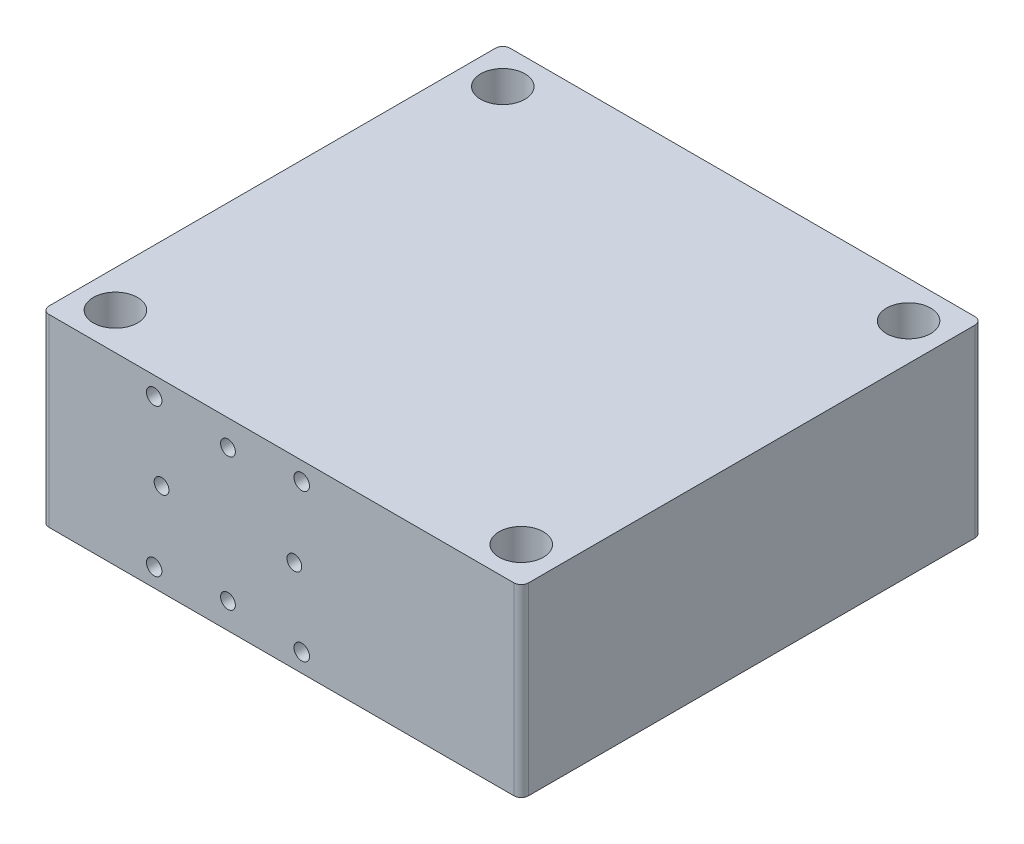
SolidWorks part; units mm, degrees
ref_plane "Front" through (0, 0, 0) normal (0, 0, 1) x (1, 0, 0)
ref_plane "Top" through (0, 0, 0) normal (0, 1, 0) x (1, 0, 0)
ref_plane "Right" through (0, 0, 0) normal (1, 0, 0) x (0, 0, -1)
sketch "草图1" plane through (0, 0, 0) normal (0, 1, 0) x (1, 0, 0)
  line L1 (-65, 62.5) -> (65, 62.5)
  line L2 (-65, 62.5) -> (-65, -62.5)
  line L3 (-65, -62.5) -> (65, -62.5)
  line L4 (65, 62.5) -> (65, -62.5)
  line L5 (-65, 62.5) -> (65, -62.5) construction
  line L6 (-65, -62.5) -> (65, 62.5) construction
  point P0 (0, 0)
  dimension "D1" = 125
  dimension "D2" = 130
extrude "凸台-拉伸1" add sketch "草图1" along normal blind 50
sketch "草图2" plane through (0, 50, 0) normal (0, 1, 0) x (1, 0, 0)
  line L1 (-55, 52.5) -> (55, 52.5) construction
  line L2 (-55, 52.5) -> (-55, -52.5) construction
  line L3 (-55, -52.5) -> (55, -52.5) construction
  line L4 (55, 52.5) -> (55, -52.5) construction
  line L5 (-55, 52.5) -> (55, -52.5) construction
  line L6 (-55, -52.5) -> (55, 52.5) construction
  circle A0 centre (-55, 52.5) radius 6
  circle A1 centre (55, 52.5) radius 6
  circle A2 centre (55, -52.5) radius 6
  circle A3 centre (-55, -52.5) radius 6
  point P0 (0, 0)
  dimension "D3" = 12
  dimension "D4" = 12
  dimension "D5" = 12
  dimension "D6" = 12
  dimension "D1" = 105
  dimension "D2" = 110
extrude "切除-拉伸1" cut sketch "草图2" against normal through all
fillet "圆角1" radius 2 4 edges at (-65, 25, 62.5) (-65, 25, -62.5) (65, 25, -62.5) (65, 25, 62.5)
sketch "草图4" plane through (0, 0, 0) normal (0, -1, 0) x (1, 0, 0)
  line L0 (-65, -60.5) -> (-65, 60.5) construction
  line L1 (-63, 62.5) -> (63, 62.5) construction
  circle A0 centre (-35, -27.5) radius 11.5
  circle A1 centre (5, 2.5) radius 11.5
  dimension "D1" = 23
  dimension "D2" = 30
  dimension "D3" = 70
  dimension "D4" = 90
  dimension "D5" = 60
extrude "切除-拉伸2" cut sketch "草图4" against normal blind 2
hole_wizard "大小mm 暗销孔4" positions "草图6" profile "草图7" hole size "Ø1.0" standard "GB"
sketch "草图6" plane through (0, 2, 0) normal (0, -1, 0) x (-1, 0, 0)
  point P0 (-5, -2.5)
sketch "草图7" plane through (5, 2, 2.5) normal (1, 0, 0) x (0, 0, -1)
  line L0 (0, 0) -> (0, 28.3047)
  line L1 (0, 28.3047) -> (5.5, 25)
  line L2 (5.5, 25) -> (5.5, 0)
  line L5 (5.5, 0) -> (0, 0)
  line L10 (0, 28.3047) -> (-5.5, 25) construction
  line L11 (0, -6.35) -> (0, 107.95) construction
  dimension "孔直径" = 11
  dimension "孔深度" = 25
  dimension "导头角度" = 118
hole_wizard "大小mm 暗销孔4" positions "草图8" profile "草图9" hole size "Ø1.0" standard "GB"
sketch "草图8" plane through (0, 2, 0) normal (0, -1, 0) x (-1, 0, 0)
  point P0 (35, 27.5)
sketch "草图9" plane through (-35, 2, -27.5) normal (1, 0, 0) x (0, 0, -1)
  line L0 (0, 0) -> (0, 28.3047)
  line L1 (0, 28.3047) -> (5.5, 25)
  line L2 (5.5, 25) -> (5.5, 0)
  line L5 (5.5, 0) -> (0, 0)
  line L10 (0, 28.3047) -> (-5.5, 25) construction
  line L11 (0, -6.35) -> (0, 107.95) construction
  dimension "孔直径" = 11
  dimension "孔深度" = 25
  dimension "导头角度" = 118
sketch "草图5" plane through (0, 0, 62.5) normal (0, 0, 1) x (1, 0, 0)
  line L0 (-14.5, 48.5615) -> (-14.5, 1.4385) construction
  line L1 (-34.5, 45) -> (5.5, 45) construction
  line L2 (-34.5, 45) -> (-34.5, 5) construction
  line L3 (-34.5, 5) -> (5.5, 5) construction
  line L4 (5.5, 45) -> (5.5, 5) construction
  line L5 (-38.4133, 25) -> (9.4133, 25) construction
  line L6 (-63, 50) -> (-63, 0) construction
  line L7 (-63, 0) -> (63, 0) construction
  circle A0 centre (-14.5, 25) radius 18 construction
  circle A1 centre (-14.5, 43) radius 2
  circle A2 centre (3.5, 25) radius 2
  circle A3 centre (-14.5, 7) radius 2
  circle A4 centre (-32.5, 25) radius 2
  point P22 (0, 0)
  dimension "D3" = 36
  dimension "D4" = 4
  dimension "D5" = 4
  dimension "D6" = 4
  dimension "D7" = 4
  dimension "D1" = 40
  dimension "D2" = 40
  dimension "D8" = 30.5
  dimension "D9" = 5
  dimension "D10" = 20
  dimension "D11" = 20
hole_wizard "M5 螺纹孔1" positions "草图10" profile "草图11" tap size "M5" standard "GB"
sketch "草图10" plane through (0, 0, 62.5) normal (0, 0, 1) x (1, 0, 0)
  point P0 (-34.5, 45)
  point P3 (5.5, 45)
  point P6 (5.5, 5)
  point P9 (-34.5, 5)
sketch "草图11" plane through (-34.5, 45, 62.5) normal (1, 0, 0) x (0, -1, 0)
  line L0 (0, 0) -> (0, 13.2618)
  line L1 (0, 13.2618) -> (2.1, 12)
  line L2 (2.1, 12) -> (2.1, 0)
  line L5 (2.1, 0) -> (0, 0)
  line L10 (0, 13.2618) -> (-2.1, 12) construction
  line L11 (0, -6.35) -> (0, 107.95) construction
  dimension "螺纹孔钻头直径" = 4.2
  dimension "螺纹孔钻头深度" = 12
  dimension "导头角度" = 118
cosmetic thread "孔螺蚊线1" parameters "D1"=10, "D2"=5
cosmetic thread "孔螺蚊线2" parameters "D1"=10, "D2"=5
cosmetic thread "孔螺蚊线3" parameters "D1"=10, "D2"=5
cosmetic thread "孔螺蚊线4" parameters "D1"=10, "D2"=5
hole_wizard "大小mm 暗销孔3" positions "草图12" profile "草图13" hole size "Ø1.0" standard "GB"
sketch "草图12" plane through (0, 0, 62.5) normal (0, 0, 1) x (1, 0, 0)
  point P0 (3.5, 25)
  point P8 (0, 0)
sketch "草图13" plane through (3.5, 25, 62.5) normal (1, 0, 0) x (0, -1, 0)
  line L0 (0, 0) -> (0, 57.2017)
  line L1 (0, 57.2017) -> (2, 56)
  line L2 (2, 56) -> (2, 0)
  line L5 (2, 0) -> (0, 0)
  line L10 (0, 57.2017) -> (-2, 56) construction
  line L11 (0, -6.35) -> (0, 107.95) construction
  dimension "孔直径" = 4
  dimension "孔深度" = 56
  dimension "导头角度" = 118
hole_wizard "大小mm 暗销孔4" positions "草图14" profile "草图15" hole size "Ø1.0" standard "GB"
sketch "草图14" plane through (0, 0, 62.5) normal (0, 0, 1) x (1, 0, 0)
  point P0 (-32.5, 25)
sketch "草图15" plane through (-32.5, 25, 62.5) normal (1, 0, 0) x (0, -1, 0)
  line L0 (0, 0) -> (0, 88.2017)
  line L1 (0, 88.2017) -> (2, 87)
  line L2 (2, 87) -> (2, 0)
  line L5 (2, 0) -> (0, 0)
  line L10 (0, 88.2017) -> (-2, 87) construction
  line L11 (0, -6.35) -> (0, 107.95) construction
  dimension "孔直径" = 4
  dimension "孔深度" = 87
  dimension "导头角度" = 118
hole_wizard "大小mm 暗销孔5" positions "草图16" profile "草图17" hole size "Ø1.0" standard "GB" end condition through all
sketch "草图16" plane through (0, 0, 62.5) normal (0, 0, 1) x (1, 0, 0)
  point P0 (-14.5, 43)
  point P3 (-14.5, 7)
sketch "草图17" plane through (-14.5, 43, 62.5) normal (1, 0, 0) x (0, -1, 0)
  line L0 (0, 0) -> (0, 125)
  line L1 (0, 125) -> (2, 125)
  line L2 (2, 125) -> (2, 0)
  line L5 (2, 0) -> (0, 0)
  line L11 (0, -6.35) -> (0, 107.95) construction
  dimension "通孔孔直径" = 4
  dimension "通孔孔深度" = 125
hole_wizard "M10x1.0 螺纹孔1" positions "草图18" profile "草图19" tap size "M10x1.0" standard "GB"
sketch "草图18" plane through (0, 0, -62.5) normal (0, 0, -1) x (-1, 0, 0)
  point P0 (14.5, 43)
  point P5 (14.5, 7)
  point P8 (0, 0)
sketch "草图19" plane through (-14.5, 43, -62.5) normal (1, 0, 0) x (0, 1, 0)
  line L0 (0, 0) -> (0, 16.7039)
  line L1 (0, 16.7039) -> (4.5, 14)
  line L2 (4.5, 14) -> (4.5, 0)
  line L5 (4.5, 0) -> (0, 0)
  line L10 (0, 16.7039) -> (-4.5, 14) construction
  line L11 (0, -6.35) -> (0, 107.95) construction
  dimension "螺纹孔钻头直径" = 9
  dimension "螺纹孔钻头深度" = 14
  dimension "导头角度" = 118
cosmetic thread "孔螺蚊线5" parameters "D1"=12, "D2"=10
cosmetic thread "孔螺蚊线6" parameters "D1"=12, "D2"=10
